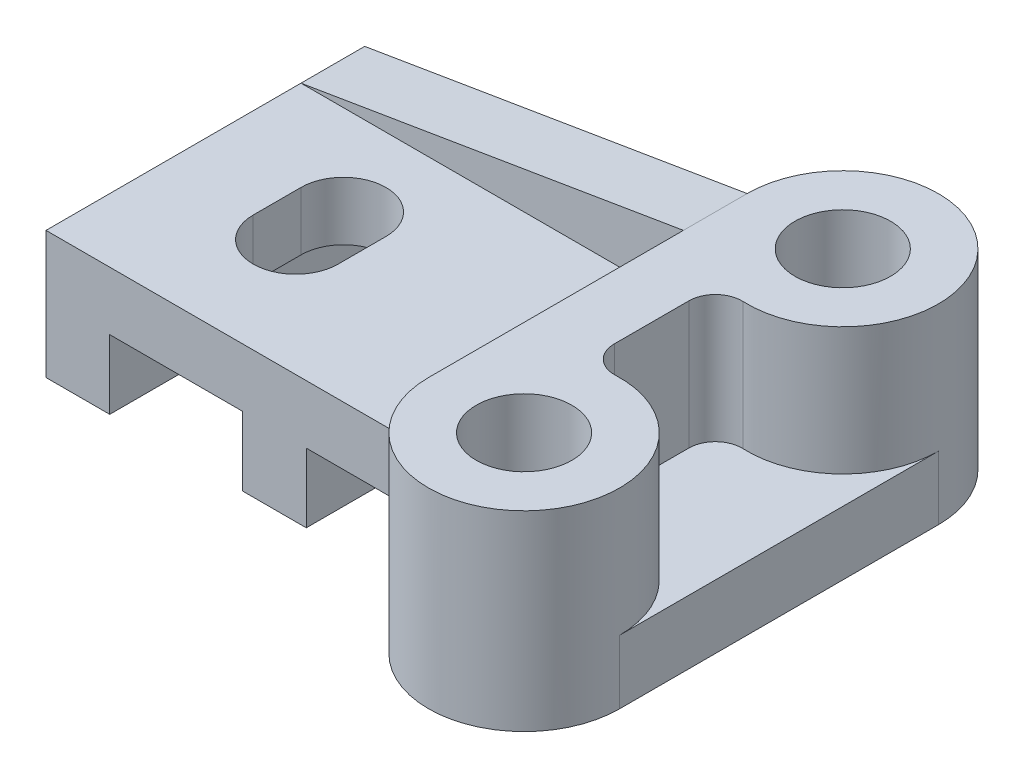
SolidWorks part; units mm, degrees
material "AISI 304"
ref_plane "Front Plane" through (0, 0, 0) normal (0, 0, 1) x (1, 0, 0)
ref_plane "Top Plane" through (0, 0, 0) normal (0, 1, 0) x (1, 0, 0)
ref_plane "Right Plane" through (0, 0, 0) normal (1, 0, 0) x (0, 0, -1)
sketch "Sketch1" plane through (0, 0, 0) normal (0, 0, 1) x (1, 0, 0)
  line L0 (0, 0) -> (0, 24)
  line L1 (0, 24) -> (72, 24)
  line L2 (0, 0) -> (12, 0)
  line L3 (12, 0) -> (12, 13)
  line L4 (12, 13) -> (37, 13)
  line L5 (37, 13) -> (37, 0)
  line L6 (37, 0) -> (49, 0)
  line L7 (49, 0) -> (49, 13)
  line L8 (49, 13) -> (72, 13)
  line L9 (72, 13) -> (72, 24)
  dimension "D1" = 24
  dimension "D2" = 12
  dimension "D3" = 72
  dimension "D4" = 13
  dimension "D5" = 25
extrude "Boss-Extrude1" add sketch "Sketch1" along normal mid plane 60
sketch "Sketch2" plane through (0, 24, 0) normal (0, 1, 0) x (1, 0, 0)
  line L0 (0, 0) -> (110.4153, 0) construction
  line L1 (72, -30) -> (72, 30) construction
  line L2 (72, 30) -> (72, -30)
  line L3 (84, 13.0294) -> (84, -13.0294)
  circle A0 centre (90, 30) radius 9
  circle A1 centre (90, -30) radius 9
  arc A2 (84, 13.0294) -> (72, 30) centre (90, 30) ccw
  arc A3 (72, -30) -> (84, -13.0294) centre (90, -30) ccw
  dimension "D1" = 18
  dimension "D2" = 18
  dimension "D3" = 60
  dimension "D4" = 18
  dimension "D5" = 12
extrude "Boss-Extrude2" add sketch "Sketch2" along normal blind 12 and the other way blind 24
fillet "Fillet1" radius 5 2 edges at (84, 18, 13.0294) (84, 18, -13.0294)
sketch "Sketch3" plane through (0, 0, 0) normal (0, -1, 0) x (1, 0, 0)
  line L0 (108, 30) -> (108, -30)
  line L1 (84, 7.0217) -> (84, -7.0217) construction
  line L2 (84, 7.0217) -> (84, -7.0217)
  arc A0 (89.2174, 12.017) -> (72, 30) centre (90, 30) ccw construction
  arc A1 (72, -30) -> (89.2174, -12.017) centre (90, -30) ccw construction
  arc A2 (89.2174, 12.017) -> (84, 7.0217) centre (89, 7.0217) ccw construction
  arc A3 (84, -7.0217) -> (89.2174, -12.017) centre (89, -7.0217) ccw construction
  arc A4 (89.2174, 12.017) -> (108, 30) centre (90, 30) ccw
  arc A5 (89.2174, 12.017) -> (84, 7.0217) centre (89, 7.0217) ccw
  arc A6 (84, -7.0217) -> (89.2174, -12.017) centre (89, -7.0217) ccw
  arc A7 (108, -30) -> (89.2174, -12.017) centre (90, -30) ccw
extrude "Boss-Extrude3" add sketch "Sketch3" against normal blind 12
sketch "Sketch4" plane through (0, 0, -30) normal (0, 0, -1) x (-1, 0, 0)
  line L0 (-72, 36) -> (0, 24)
rib "Rib1" sketch "Sketch4" sketch "Sketch4" thickness 12 extrusion direction parallel to sketch draft on no parameters "D1"=12
sketch "Sketch5" plane through (0, 24, 0) normal (0, 1, 0) x (1, 0, 0)
  line L0 (25, 1) -> (25, -8) construction
  line L1 (33, 1) -> (33, -8)
  line L2 (17, 1) -> (17, -8)
  line L4 (72, -30) -> (0, -30) construction
  line L5 (0, -30) -> (0, 18) construction
  arc A0 (33, 1) -> (17, 1) centre (25, 1) ccw
  arc A1 (17, -8) -> (33, -8) centre (25, -8) ccw
  point P2 (25, -3.5)
  dimension "D1" = 8
  dimension "D2" = 9
  dimension "D3" = 22
  dimension "D4" = 25
extrude "Cut-Extrude1" cut sketch "Sketch5" against normal through all
